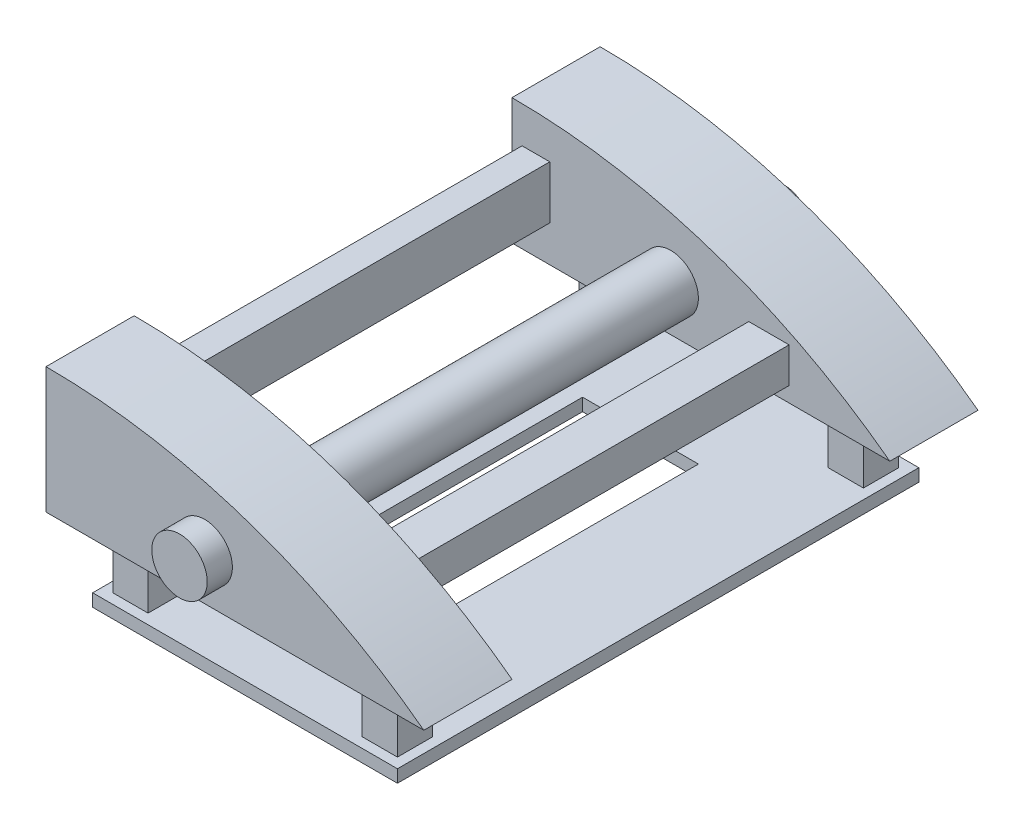
SolidWorks part; units mm, degrees
ref_plane "Ön Düzlem" through (0, 0, 0) normal (0, 0, 1) x (1, 0, 0)
ref_plane "Üst Düzlem" through (0, 0, 0) normal (0, 1, 0) x (1, 0, 0)
ref_plane "Sağ Düzlem" through (0, 0, 0) normal (1, 0, 0) x (0, 0, -1)
sketch "Sketch1" plane through (0, 0, 0) normal (0, 0, 1) x (1, 0, 0)
  line L0 (0, 0) -> (150, 0)
  line L1 (0, 0) -> (0, 50)
  arc A0 (0, 50) -> (150, 0) centre (0, -200) cw
  dimension "D1" = 50
  dimension "D2" = 150
extrude "Boss-Extrude1" add sketch "Sketch1" along normal blind 35
sketch "Sketch2" plane through (0, 0, 35) normal (0, 0, 1) x (1, 0, 0)
  line L0 (0, 0) -> (150, 0) construction
  line L1 (15, 14.4246) -> (4, 14.4246)
  line L2 (15, 14.4246) -> (15, 35.4246)
  line L3 (15, 35.4246) -> (4, 35.4246)
  line L4 (4, 14.4246) -> (4, 35.4246)
  line L5 (15, 14.4246) -> (4, 35.4246) construction
  line L6 (15, 35.4246) -> (4, 14.4246) construction
  line L7 (0, 50) -> (0, 0) construction
  point P0 (9.5, 24.9246)
  dimension "D1" = 21
  dimension "D2" = 11
  dimension "D3" = 14.4246
  dimension "D4" = 4
extrude "Boss-Extrude3" add sketch "Sketch2" along normal blind 150
sketch "Sketch3" plane through (0, 0, 185) normal (0, 0, 1) x (1, 0, 0)
  line L0 (150, 0) -> (0, 0)
  line L1 (0, 0) -> (0, 50)
  arc A0 (0, 50) -> (150, 0) centre (0, -200) cw
extrude "Boss-Extrude4" add sketch "Sketch3" along normal blind 35
sketch "Sketch4" plane through (0, 0, 185) normal (0, 0, -1) x (-1, 0, 0)
  line L0 (0, 0) -> (-150, 0) construction
  line L1 (-110, 6) -> (-94, 6)
  line L2 (-110, 6) -> (-110, 20)
  line L3 (-110, 20) -> (-94, 20)
  line L4 (-94, 6) -> (-94, 20)
  line L5 (-110, 6) -> (-94, 20) construction
  line L6 (-110, 20) -> (-94, 6) construction
  line L7 (0, 50) -> (0, 0) construction
  point P0 (-102, 13)
  point P7 (-110, 13)
  dimension "D1" = 14
  dimension "D2" = 16
  dimension "D3" = 6
  dimension "D4" = 110
extrude "Boss-Extrude5" add sketch "Sketch4" along normal blind 150
sketch "Sketch5" plane through (0, 0, 0) normal (0, -1, 0) x (1, 0, 0)
  line L0 (0, 185) -> (150, 185) construction
  line L1 (16, 195.4822) -> (30, 195.4822)
  line L2 (16, 195.4822) -> (16, 209.4822)
  line L3 (16, 209.4822) -> (30, 209.4822)
  line L4 (30, 195.4822) -> (30, 209.4822)
  line L5 (16, 195.4822) -> (30, 209.4822) construction
  line L6 (16, 209.4822) -> (30, 195.4822) construction
  line L7 (0, 220) -> (0, 185) construction
  line L8 (0, 35) -> (0, 0) construction
  line L9 (16, 10.48) -> (30, 10.48)
  line L10 (16, 10.48) -> (16, 24.48)
  line L11 (16, 24.48) -> (30, 24.48)
  line L12 (30, 10.48) -> (30, 24.48)
  line L13 (16, 10.48) -> (30, 24.48) construction
  line L14 (16, 24.48) -> (30, 10.48) construction
  line L15 (0, 0) -> (150, 0) construction
  line L16 (150, 220) -> (150, 185) construction
  line L17 (115, 195.4822) -> (129, 195.4822)
  line L18 (115, 195.4822) -> (115, 209.4822)
  line L19 (115, 209.4822) -> (129, 209.4822)
  line L20 (129, 195.4822) -> (129, 209.4822)
  line L21 (115, 195.4822) -> (129, 209.4822) construction
  line L22 (115, 209.4822) -> (129, 195.4822) construction
  line L23 (150, 35) -> (150, 0) construction
  line L24 (115, 10.48) -> (129, 10.48)
  line L25 (115, 10.48) -> (115, 24.48)
  line L26 (115, 24.48) -> (129, 24.48)
  line L27 (129, 10.48) -> (129, 24.48)
  line L28 (115, 10.48) -> (129, 24.48) construction
  line L29 (115, 24.48) -> (129, 10.48) construction
  point P0 (23, 202.4822)
  point P9 (23, 17.48)
  point P18 (122, 202.4822)
  point P25 (122, 17.48)
  dimension "D1" = 14
  dimension "D2" = 14
  dimension "D3" = 10.4822
  dimension "D4" = 16
  dimension "D5" = 16
  dimension "D6" = 10.48
  dimension "D7" = 14
  dimension "D8" = 14
  dimension "D9" = 10.4822
  dimension "D10" = 21
  dimension "D11" = 14
  dimension "D12" = 14
  dimension "D13" = 14
  dimension "D14" = 14
  dimension "D15" = 21
  dimension "D16" = 10.48
extrude "Boss-Extrude6" add sketch "Sketch5" along normal blind 25
sketch "Sketch6" plane through (0, -25, 0) normal (0, -1, 0) x (-1, 0, 0)
  line L0 (-16, -10.48) -> (-30, -10.48) construction
  line L1 (-12, -213.4822) -> (-133, -213.4822)
  line L2 (-12, -213.4822) -> (-12, -6.48)
  line L3 (-12, -6.48) -> (-133, -6.48)
  line L4 (-133, -213.4822) -> (-133, -6.48)
  line L5 (-16, -24.48) -> (-16, -10.48) construction
  line L7 (-129, -10.48) -> (-129, -24.48) construction
  line L8 (-129, -209.4822) -> (-115, -209.4822) construction
  dimension "D1" = 4
  dimension "D2" = 4
  dimension "D3" = 4
  dimension "D4" = 4
extrude "Boss-Extrude7" add sketch "Sketch6" along normal blind 5
sketch "Sketch7" plane through (0, 0, 0) normal (0, 0, -1) x (-1, 0, 0)
  line L0 (0, 0) -> (-150, 0) construction
  line L1 (0, 50) -> (0, 0) construction
  circle A0 centre (-63, 18) radius 11
  dimension "D1" = 22
  dimension "D2" = 18
  dimension "D3" = 63
extrude "Boss-Extrude8" add sketch "Sketch7" against normal blind 230 and the other way blind 10
sketch "Sketch8" plane through (0, -30, 0) normal (0, -1, 0) x (1, 0, 0)
  line L0 (133, 213.4822) -> (12, 213.4822) construction
  line L1 (42, 170.9822) -> (88, 170.9822)
  line L2 (42, 170.9822) -> (42, 48.9822)
  line L3 (42, 48.9822) -> (88, 48.9822)
  line L4 (88, 170.9822) -> (88, 48.9822)
  line L7 (12, 213.4822) -> (12, 6.48) construction
  dimension "D1" = 46
  dimension "D2" = 122
  dimension "D3" = 42.5
  dimension "D4" = 30
extrude "Cut-Extrude1" cut sketch "Sketch8" against normal blind 5
sketch "Sketch9" plane through (0, 0, 230) normal (0, 0, 1) x (1, 0, 0)
  circle A0 centre (63, 18) radius 30
  dimension "D1" = 60
